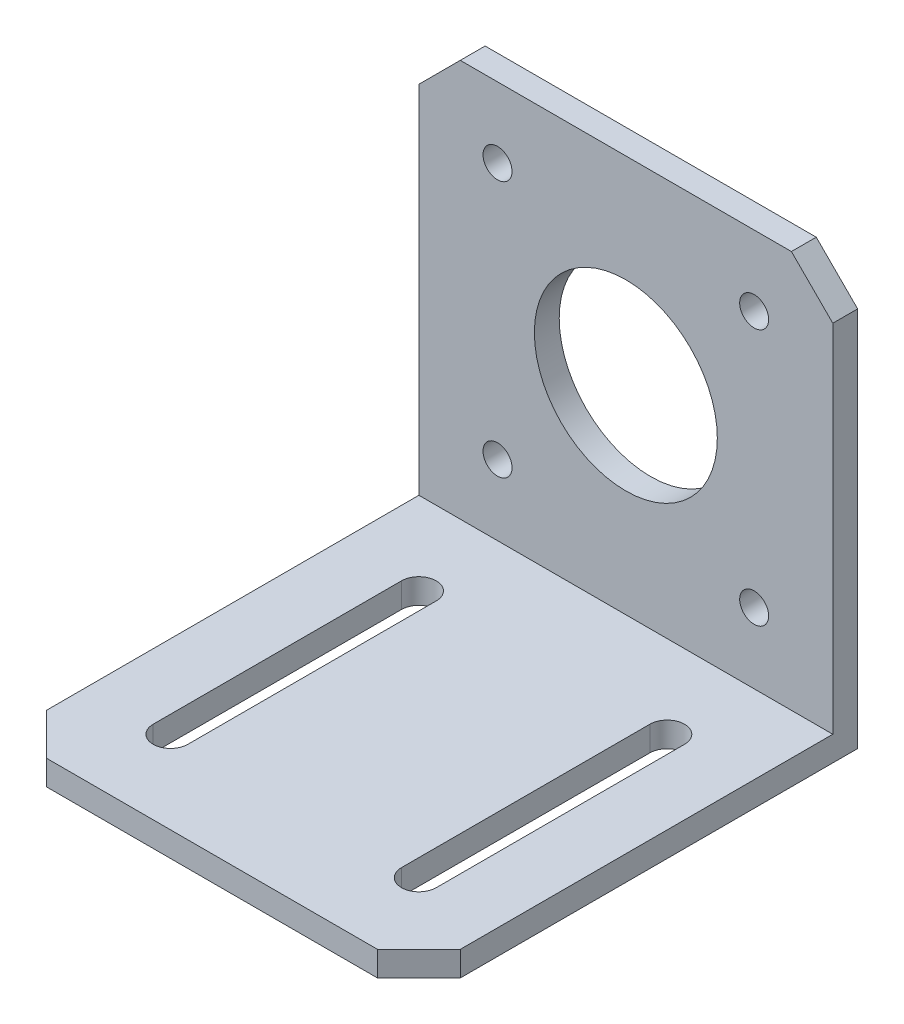
SolidWorks part; units mm, degrees
ref_plane "Front Plane" through (0, 0, 0) normal (0, 0, 1) x (1, 0, 0)
ref_plane "Top Plane" through (0, 0, 0) normal (0, 1, 0) x (1, 0, 0)
ref_plane "Right Plane" through (0, 0, 0) normal (1, 0, 0) x (0, 0, -1)
sketch "Sketch1" plane through (0, 0, 0) normal (1, 0, 0) x (0, 0, -1)
  line L0 (0, 0) -> (0, 3)
  line L1 (0, 3) -> (50, 3)
  line L2 (50, 3) -> (50, 51)
  line L3 (50, 51) -> (53, 51)
  line L4 (53, 51) -> (53, 0)
  line L5 (53, 0) -> (0, 0)
  dimension "D1" = 53
  dimension "D2" = 51
  dimension "D3" = 3
extrude "Boss-Extrude1" add sketch "Sketch1" against normal blind 50
sketch "Sketch2" plane through (0, 0, -50) normal (0, 0, 1) x (1, 0, 0)
  line L0 (-25, 51) -> (-25, 3) construction
  line L1 (-50, 51) -> (0, 51) construction
  line L2 (-50, 3) -> (0, 3) construction
  line L3 (-50, 27) -> (0, 27) construction
  line L4 (-50, 51) -> (-50, 3) construction
  line L5 (0, 51) -> (0, 3) construction
  circle A0 centre (-25, 27) radius 11.05
  circle A1 centre (-40.5, 42.5) radius 1.75
  circle A2 centre (-9.5, 42.5) radius 1.75
  circle A3 centre (-9.5, 11.5) radius 1.75
  circle A4 centre (-40.5, 11.5) radius 1.75
  dimension "D3" = 3.5
  dimension "D4" = 22.1
  dimension "D1" = 31
  dimension "D2" = 31
extrude "Cut-Extrude1" cut sketch "Sketch2" against normal up to next
sketch "Sketch3" plane through (0, 3, 0) normal (0, 1, 0) x (1, 0, 0)
  line L0 (-25, 50) -> (-25, 0) construction
  line L1 (-50, 50) -> (0, 50) construction
  line L2 (-50, 0) -> (0, 0) construction
  line L3 (-50, 25) -> (0, 25) construction
  line L4 (-50, 50) -> (-50, 0) construction
  line L5 (0, 50) -> (0, 0) construction
  line L6 (-40, 40) -> (-40, 10) construction
  line L7 (-37.9, 40) -> (-37.9, 10)
  line L8 (-42.1, 40) -> (-42.1, 10)
  line L9 (-10, 40) -> (-10, 10) construction
  line L10 (-12.1, 40) -> (-12.1, 10)
  line L11 (-7.9, 40) -> (-7.9, 10)
  arc A0 (-37.9, 40) -> (-42.1, 40) centre (-40, 40) ccw
  arc A1 (-42.1, 10) -> (-37.9, 10) centre (-40, 10) ccw
  arc A2 (-12.1, 40) -> (-7.9, 40) centre (-10, 40) cw
  arc A3 (-7.9, 10) -> (-12.1, 10) centre (-10, 10) cw
  point P14 (-40, 25)
  point P21 (-10, 25)
  dimension "D1" = 30
  dimension "D2" = 30
  dimension "D3" = 4.2
extrude "Cut-Extrude2" cut sketch "Sketch3" against normal up to next
chamfer "Chamfer1" distance 5 angle 45 4 edges at (-50, 51, -51.5) (0, 51, -51.5) (0, 1.5, 0) (-50, 1.5, 0)
